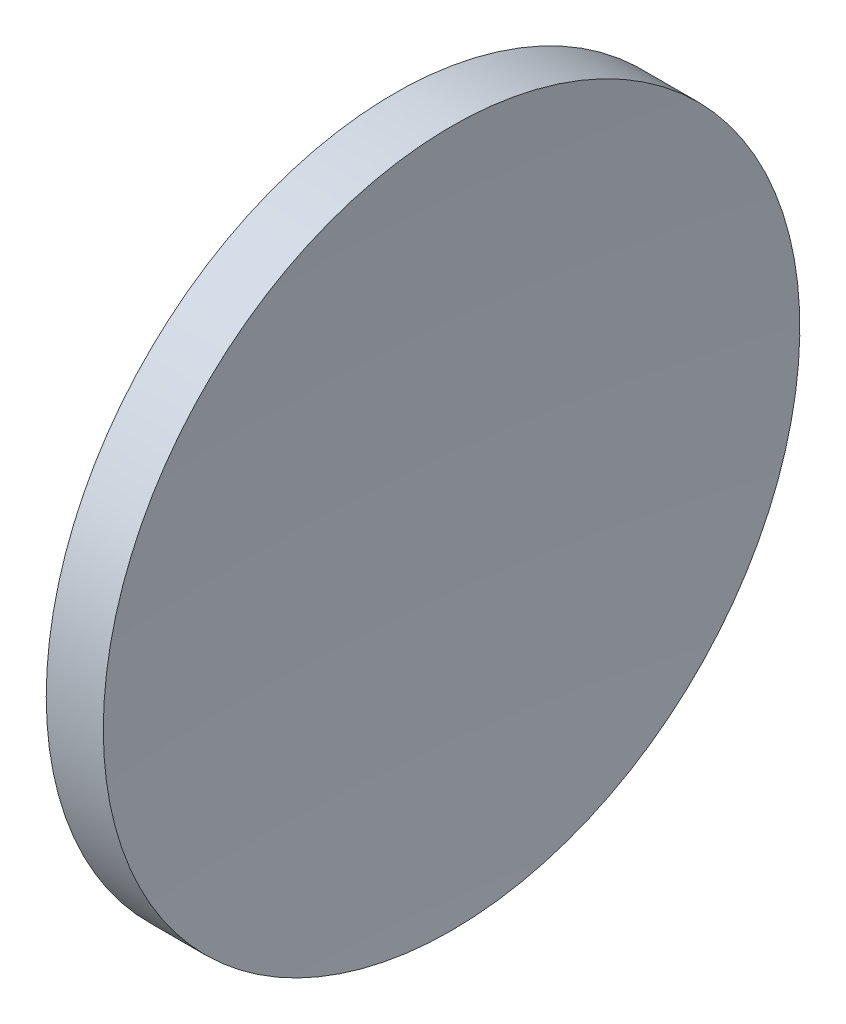
SolidWorks part; units mm, degrees
ref_plane "前视基准面" through (0, 0, 0) normal (0, 0, 1) x (1, 0, 0)
ref_plane "上视基准面" through (0, 0, 0) normal (0, 1, 0) x (1, 0, 0)
ref_plane "右视基准面" through (0, 0, 0) normal (1, 0, 0) x (0, 0, -1)
sketch "草图1" plane through (0, 0, 0) normal (0, 0, 1) x (1, 0, 0)
  line L0 (105.6218, 65.1556) -> (137.1869, 65.1556) construction
  line L1 (113.9119, 65.1556) -> (113.9119, 85.1556)
  line L2 (116.4119, 65.1556) -> (113.9119, 65.1556)
  line L3 (113.9119, 85.1556) -> (117.1878, 85.1556)
  arc A0 (117.1878, 85.1556) -> (116.4119, 65.1556) centre (374.5919, 65.1556) ccw
revolve "旋转1" add sketch "草图1" angle 360 about L0
